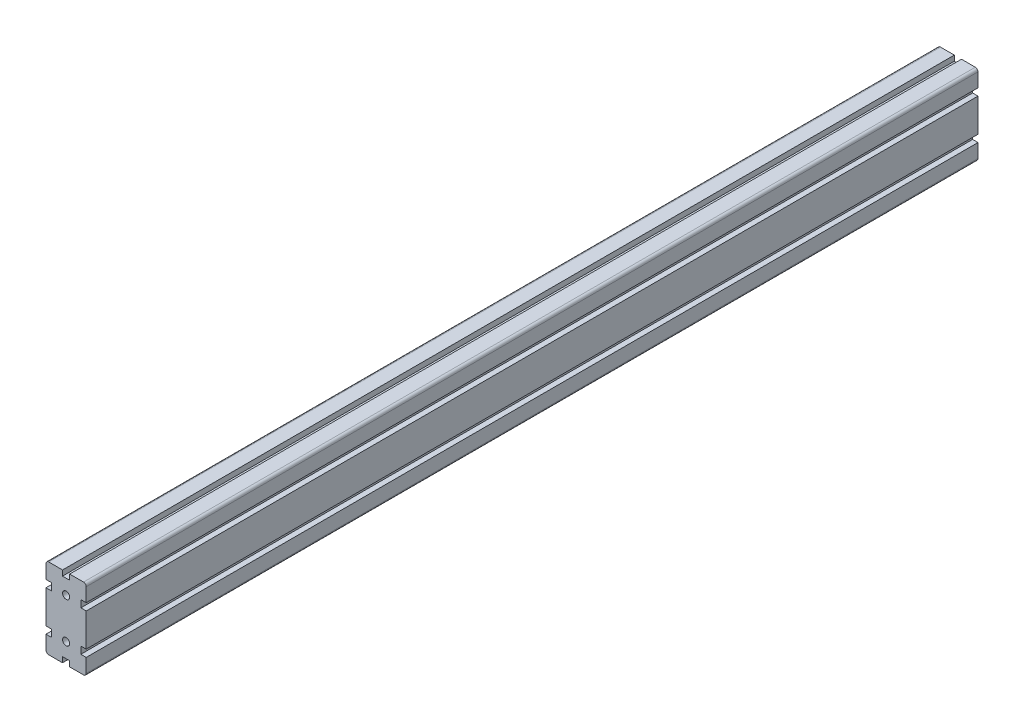
SolidWorks part; units mm, degrees
ref_plane "Plan de face" through (0, 0, 0) normal (0, 0, 1) x (1, 0, 0)
ref_plane "Plan de dessus" through (0, 0, 0) normal (0, 1, 0) x (1, 0, 0)
ref_plane "Plan de droite" through (0, 0, 0) normal (1, 0, 0) x (0, 0, -1)
ref_plane "Plan1" through (0, 0, -1000) normal (0, 0, -1) x (-1, 0, 0)
sketch "Esquisse1" plane through (0, 0, -1000) normal (0, 0, -1) x (-1, 0, 0)
  line L0 (42.2889, 57.3154) -> (48.2889, 57.3154)
  line L1 (48.2889, 57.3154) -> (48.2889, 72.8154)
  line L2 (45.2889, 75.8154) -> (29.7889, 75.8154)
  line L3 (29.7889, 75.8154) -> (29.7889, 69.8154)
  line L4 (25.7889, 53.3154) -> (25.7889, 8.3154) construction
  line L5 (25.7889, 53.3154) -> (38.7568, 53.3154) construction
  line L6 (25.7889, 8.3154) -> (38.7568, 8.3154) construction
  line L10 (21.7889, 69.8154) -> (21.7889, 75.8154)
  line L11 (21.7889, 75.8154) -> (6.2889, 75.8154)
  line L12 (3.2889, 72.8154) -> (3.2889, 57.3154)
  line L13 (3.2889, 57.3154) -> (9.2889, 57.3154)
  line L20 (9.2889, 49.3154) -> (3.2889, 49.3154)
  line L21 (3.2889, 49.3154) -> (3.2889, 12.3154)
  line L22 (21.7889, -8.1846) -> (29.7889, -8.1846)
  line L23 (42.2889, 12.3154) -> (42.2889, 4.3154)
  line L24 (9.2889, 12.3154) -> (9.2889, 4.3154)
  line L25 (42.2889, 57.3154) -> (42.2889, 49.3154)
  line L26 (3.2889, 12.3154) -> (9.2889, 12.3154)
  line L33 (9.2889, 4.3154) -> (3.2889, 4.3154)
  line L34 (3.2889, 4.3154) -> (3.2889, -11.1846)
  line L35 (6.2889, -14.1846) -> (21.7889, -14.1846)
  line L36 (21.7889, -14.1846) -> (21.7889, -8.1846)
  line L43 (29.7889, -8.1846) -> (29.7889, -14.1846)
  line L44 (29.7889, -14.1846) -> (45.2889, -14.1846)
  line L45 (48.2889, -11.1846) -> (48.2889, 4.3154)
  line L46 (48.2889, 4.3154) -> (42.2889, 4.3154)
  line L53 (42.2889, 12.3154) -> (48.2889, 12.3154)
  line L54 (9.2889, 57.3154) -> (9.2889, 49.3154)
  line L55 (21.7889, 69.8154) -> (29.7889, 69.8154)
  line L58 (48.2889, 12.3154) -> (48.2889, 49.3154)
  line L59 (48.2889, 49.3154) -> (42.2889, 49.3154)
  arc A0 (48.2889, 72.8154) -> (45.2889, 75.8154) centre (45.2889, 72.8154) ccw
  arc A2 (6.2889, 75.8154) -> (3.2889, 72.8154) centre (6.2889, 72.8154) ccw
  arc A5 (3.2889, -11.1846) -> (6.2889, -14.1846) centre (6.2889, -11.1846) ccw
  arc A7 (45.2889, -14.1846) -> (48.2889, -11.1846) centre (45.2889, -11.1846) ccw
  circle A44 centre (25.7889, 53.3154) radius 4
  circle A45 centre (25.7889, 8.3154) radius 4
  dimension "D5" = 8
  dimension "D6" = 8
  dimension "D1" = 4
  dimension "D2" = 90
  dimension "D3" = 4
  dimension "D4" = 4
extrude "Boss.-Extru.1" add sketch "Esquisse1" against normal blind 998
